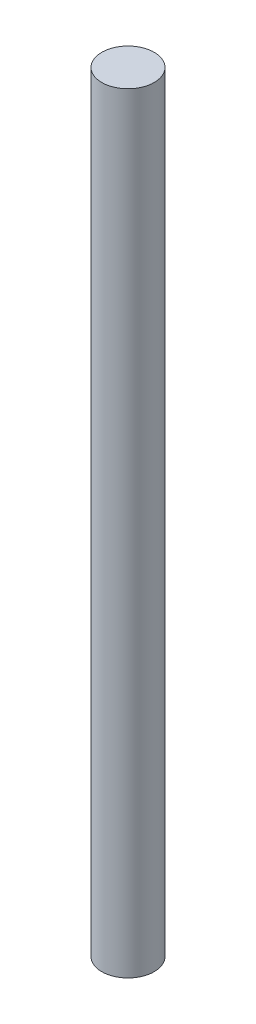
SolidWorks part; units mm, degrees
material "1060 Alloy"
ref_plane "Front Plane" through (0, 0, 0) normal (0, 0, 1) x (1, 0, 0)
ref_plane "Top Plane" through (0, 0, 0) normal (0, 1, 0) x (1, 0, 0)
ref_plane "Right Plane" through (0, 0, 0) normal (1, 0, 0) x (0, 0, -1)
sketch "Sketch1" plane through (0, 0, 0) normal (0, 1, 0) x (1, 0, 0)
  circle A0 centre (0, 0) radius 2.5
  dimension "D1" = 5
extrude "Boss-Extrude1" add sketch "Sketch1" along normal blind 73.5
